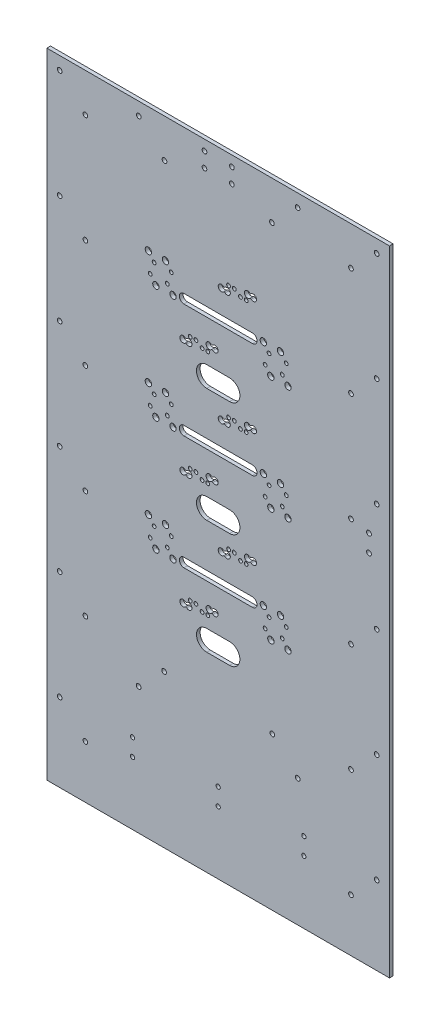
SolidWorks part; units mm, degrees
ref_plane "Front Plane" through (0, 0, 0) normal (0, 0, 1) x (1, 0, 0)
ref_plane "Top Plane" through (0, 0, 0) normal (0, 1, 0) x (1, 0, 0)
ref_plane "Right Plane" through (0, 0, 0) normal (1, 0, 0) x (0, 0, -1)
sketch "Sketch1" plane through (0, 0, 0) normal (0, 0, 1) x (1, 0, 0)
  line L0 (-165.9868, 389.7156) -> (134.0132, 389.7156) construction
  line L1 (-165.9868, 389.7156) -> (134.0132, 389.7156)
  line L2 (-165.9868, 389.7156) -> (-165.9868, -165.2844)
  line L3 (-165.9868, -165.2844) -> (134.0132, -165.2844)
  line L4 (134.0132, 389.7156) -> (134.0132, -165.2844)
  line L5 (89.0132, -165.2844) -> (134.0132, -165.2844) construction
  line L6 (134.0132, 389.7156) -> (134.0132, -165.2844) construction
  dimension "D2" = 300
extrude "Boss-Extrude1" add sketch "Sketch1" along normal blind 3.175
sketch "Sketch2" plane through (0, 0, 0) normal (0, 0, -1) x (-1, 0, 0)
  line L0 (15.9868, -165.2844) -> (15.9868, 389.7156) construction
  line L1 (165.9868, -165.2844) -> (-134.0132, -165.2844) construction
  line L2 (-134.0132, 389.7156) -> (165.9868, 389.7156) construction
  line L3 (0.9868, 59.7156) -> (30.9868, 59.7156) construction
  line L4 (0.9868, 159.7156) -> (30.9868, 159.7156) construction
  line L5 (0.9868, 259.7156) -> (30.9868, 259.7156) construction
  point P8 (15.9868, 59.7156)
  point P11 (15.9868, 159.7156)
  dimension "D1" = 30
  dimension "D2" = 30
  dimension "D3" = 100
  dimension "D4" = 100
  dimension "D5" = 130
sketch "Sketch4" plane through (0, 0, 3.175) normal (0, 0, 1) x (1, 0, 0)
  line L0 (-45.9868, 259.7156) -> (14.0132, 259.7156) construction
  line L1 (-45.9868, 263.7156) -> (14.0132, 263.7156)
  line L2 (-45.9868, 255.7156) -> (14.0132, 255.7156)
  line L3 (-15.9868, -165.2844) -> (-15.9868, 389.7156) construction
  line L4 (-0.9868, 259.7156) -> (-30.9868, 259.7156) construction
  line L5 (-45.9868, 159.7156) -> (14.0132, 159.7156) construction
  line L6 (-45.9868, 163.7156) -> (14.0132, 163.7156)
  line L7 (-45.9868, 155.7156) -> (14.0132, 155.7156)
  line L8 (-45.9868, 59.7156) -> (14.0132, 59.7156) construction
  line L9 (-45.9868, 63.7156) -> (14.0132, 63.7156)
  line L10 (-45.9868, 55.7156) -> (14.0132, 55.7156)
  line L11 (-0.9868, 59.7156) -> (-30.9868, 59.7156) construction
  line L12 (-0.9868, 159.7156) -> (-30.9868, 159.7156) construction
  arc A0 (-45.9868, 263.7156) -> (-45.9868, 255.7156) centre (-45.9868, 259.7156) ccw
  arc A1 (14.0132, 255.7156) -> (14.0132, 263.7156) centre (14.0132, 259.7156) ccw
  arc A2 (-45.9868, 163.7156) -> (-45.9868, 155.7156) centre (-45.9868, 159.7156) ccw
  arc A3 (14.0132, 155.7156) -> (14.0132, 163.7156) centre (14.0132, 159.7156) ccw
  arc A4 (-45.9868, 63.7156) -> (-45.9868, 55.7156) centre (-45.9868, 59.7156) ccw
  arc A5 (14.0132, 55.7156) -> (14.0132, 63.7156) centre (14.0132, 59.7156) ccw
  point P2 (-15.9868, 259.7156)
  point P14 (-15.9868, 159.7156)
  point P21 (-15.9868, 59.7156)
  dimension "D1" = 15
  dimension "D2" = 8
  dimension "D3" = 15
  dimension "D4" = 8
  dimension "D5" = 15
  dimension "D6" = 8
extrude "Cut-Extrude1" cut sketch "Sketch4" against normal blind 10
sketch "Sketch5" plane through (0, 0, 0) normal (0, 0, -1) x (-1, 0, 0)
  line L0 (45.9868, 155.7156) -> (-14.0132, 155.7156) construction
sketch "Sketch6" plane through (0, 0, 0) normal (0, 0, -1) x (-1, 0, 0)
  line L0 (-134.0132, 389.7156) -> (165.9868, 389.7156) construction
  circle A0 centre (3.9868, 380.7156) radius 2.05
  circle A1 centre (27.9868, 380.7156) radius 2.05
  circle A2 centre (27.9868, 367.7156) radius 2.05
  circle A3 centre (3.9868, 367.7156) radius 2.05
  point P12 (42.9868, 389.7156)
  dimension "D1" = 15
  dimension "D2" = 4.1
  dimension "D3" = 39
  dimension "D4" = 9
  dimension "D5" = 22
extrude "Cut-Extrude5" cut sketch "Sketch6" against normal blind 51
sketch "Sketch8" plane through (0, 0, 0) normal (0, 0, -1) x (-1, 0, 0)
  circle A0 centre (-116.0132, 162.9803) radius 2.1
  circle A1 centre (-116.0132, 147.9803) radius 2.1
  point P6 (0, 0)
  point P7 (0, 0)
  dimension "D1" = 4.2
extrude "Cut-Extrude7" cut sketch "Sketch8" against normal blind 67
sketch "Sketch9" plane through (0, 0, 0) normal (0, 0, -1) x (-1, 0, 0)
  line L0 (15.9868, 389.7156) -> (15.9868, 432.1874) construction
  line L1 (-134.0132, 389.7156) -> (165.9868, 389.7156) construction
  circle A0 centre (-122.7632, 378.4656) radius 2.05
  circle A1 centre (-100.2632, 355.9656) radius 2.05
  circle A2 centre (-53.5368, 378.4656) radius 2.05
  circle A3 centre (-31.0368, 355.9656) radius 2.05
  circle A4 centre (-122.7632, 283.4656) radius 2.05
  circle A5 centre (-100.2632, 260.9656) radius 2.05
  circle A6 centre (-122.7632, 188.4656) radius 2.05
  circle A7 centre (-100.2632, 165.9656) radius 2.05
  circle A8 centre (-122.7632, 93.4656) radius 2.05
  circle A9 centre (-100.2632, 70.9656) radius 2.05
  circle A10 centre (-122.7632, -1.5344) radius 2.05
  circle A11 centre (-100.2632, -24.0344) radius 2.05
  circle A12 centre (-122.7632, -96.5344) radius 2.05
  circle A13 centre (-100.2632, -119.0344) radius 2.05
  circle A14 centre (-122.7632, -191.5344) radius 2.05
  circle A15 centre (-100.2632, -214.0344) radius 2.05
  circle A16 centre (-53.6482, -54.0344) radius 2.05
  circle A17 centre (-31.371, -31.5344) radius 2.05
  circle A18 centre (63.3447, -31.5344) radius 2.05
  circle A19 centre (85.6219, -54.0344) radius 2.05
  circle A20 centre (132.2368, -214.0344) radius 2.05
  circle A21 centre (154.7368, -191.5344) radius 2.05
  circle A22 centre (132.2368, -119.0344) radius 2.05
  circle A23 centre (154.7368, -96.5344) radius 2.05
  circle A24 centre (132.2368, -24.0344) radius 2.05
  circle A25 centre (154.7368, -1.5344) radius 2.05
  circle A26 centre (132.2368, 70.9656) radius 2.05
  circle A27 centre (154.7368, 93.4656) radius 2.05
  circle A28 centre (132.2368, 165.9656) radius 2.05
  circle A29 centre (154.7368, 188.4656) radius 2.05
  circle A30 centre (132.2368, 260.9656) radius 2.05
  circle A31 centre (154.7368, 283.4656) radius 2.05
  circle A32 centre (63.0104, 355.9656) radius 2.05
  circle A33 centre (85.5104, 378.4656) radius 2.05
  circle A34 centre (132.2368, 355.9656) radius 2.05
  circle A35 centre (154.7368, 378.4656) radius 2.05
  dimension "D1" = 7
extrude "Cut-Extrude8" cut sketch "Sketch9" against normal blind 10
sketch "Sketch10" plane through (0, 0, 0) normal (0, 0, -1) x (-1, 0, 0)
  circle A0 centre (35.464, 33.6216) radius 1.651
  circle A1 centre (25.1051, 30.1602) radius 1.651
  arc A2 (43.5999, 30.6974) -> (43.5999, 26.4941) centre (41.7588, 28.5958) ccw
  arc A3 (20.6514, 37.2877) -> (20.6514, 33.0844) centre (18.8103, 35.186) ccw
  circle A4 centre (-30.1263, 38.9336) radius 2.794
  circle A5 centre (-23.5434, 61.8842) radius 2.794
  circle A6 centre (-25.1024, 45.23) radius 1.651
  circle A7 centre (-28.5672, 55.5878) radius 1.651
  circle A8 centre (-45.1263, 38.9336) radius 2.794
  circle A9 centre (-38.5434, 61.8842) radius 2.794
  circle A10 centre (-40.1024, 45.23) radius 1.651
  circle A11 centre (-43.5672, 55.5878) radius 1.651
  circle A12 centre (40.464, 33.6216) radius 1.651
  circle A13 centre (30.1051, 30.1602) radius 1.651
  arc A14 (44.9177, 26.4941) -> (44.9177, 30.6974) centre (46.7588, 28.5958) ccw
  arc A15 (21.9693, 33.0844) -> (21.9693, 37.2877) centre (23.8103, 35.186) ccw
  arc A16 (21.9693, 33.0844) -> (20.6514, 33.0844) centre (21.3103, 32.3322) ccw
  arc A17 (21.9693, 37.2877) -> (20.6514, 37.2877) centre (21.3103, 38.0399) cw
  arc A18 (44.9177, 26.4941) -> (43.5999, 26.4941) centre (44.2588, 25.7419) ccw
  arc A19 (44.9177, 30.6974) -> (43.5999, 30.6974) centre (44.2588, 31.4496) cw
  circle A40 centre (55.5171, 57.5469) radius 2.794
  circle A41 centre (70.5171, 57.5469) radius 2.794
  circle A42 centre (75.5409, 63.8433) radius 1.651
  circle A43 centre (60.5409, 63.8433) radius 1.651
  circle A44 centre (-3.4904, 85.8095) radius 1.651
  circle A45 centre (6.8686, 89.271) radius 1.651
  arc A46 (-11.6262, 88.7337) -> (-11.6262, 92.937) centre (-9.7851, 90.8353) ccw
  arc A47 (11.3223, 82.1435) -> (11.3223, 86.3468) centre (13.1633, 84.2451) ccw
  circle A48 centre (62.0999, 80.4975) radius 2.794
  circle A49 centre (57.0761, 74.2011) radius 1.651
  circle A50 centre (77.0999, 80.4975) radius 2.794
  circle A51 centre (72.0761, 74.2011) radius 1.651
  circle A52 centre (-8.4904, 85.8095) radius 1.651
  circle A53 centre (1.8686, 89.271) radius 1.651
  arc A54 (-12.9441, 92.937) -> (-12.9441, 88.7337) centre (-14.7851, 90.8353) ccw
  arc A55 (10.0044, 86.3468) -> (10.0044, 82.1435) centre (8.1633, 84.2451) ccw
  arc A56 (10.0044, 86.3468) -> (11.3223, 86.3468) centre (10.6633, 87.099) ccw
  arc A57 (10.0044, 82.1435) -> (11.3223, 82.1435) centre (10.6633, 81.3913) cw
  arc A58 (-12.9441, 92.937) -> (-11.6262, 92.937) centre (-12.2851, 93.6892) ccw
  arc A59 (-12.9441, 88.7337) -> (-11.6262, 88.7337) centre (-12.2851, 87.9815) cw
  circle A60 centre (63.0104, 355.9656) radius 2.05 construction
  circle A62 centre (35.464, 133.6216) radius 1.651
  circle A63 centre (25.1051, 130.1602) radius 1.651
  arc A64 (43.5999, 130.6974) -> (43.5999, 126.4941) centre (41.7588, 128.5958) ccw
  arc A65 (20.6514, 137.2877) -> (20.6514, 133.0844) centre (18.8103, 135.186) ccw
  circle A66 centre (-30.1263, 138.9336) radius 2.794
  circle A67 centre (-23.5434, 161.8842) radius 2.794
  circle A68 centre (-25.1024, 145.23) radius 1.651
  circle A69 centre (-28.5672, 155.5878) radius 1.651
  circle A70 centre (-45.1263, 138.9336) radius 2.794
  circle A71 centre (-38.5434, 161.8842) radius 2.794
  circle A72 centre (-40.1024, 145.23) radius 1.651
  circle A73 centre (-43.5672, 155.5878) radius 1.651
  circle A74 centre (40.464, 133.6216) radius 1.651
  circle A75 centre (30.1051, 130.1602) radius 1.651
  arc A76 (44.9177, 126.4941) -> (44.9177, 130.6974) centre (46.7588, 128.5958) ccw
  arc A77 (21.9693, 133.0844) -> (21.9693, 137.2877) centre (23.8103, 135.186) ccw
  arc A78 (21.9693, 133.0844) -> (20.6514, 133.0844) centre (21.3103, 132.3322) ccw
  arc A79 (21.9693, 137.2877) -> (20.6514, 137.2877) centre (21.3103, 138.0399) cw
  arc A80 (44.9177, 126.4941) -> (43.5999, 126.4941) centre (44.2588, 125.7419) ccw
  arc A81 (44.9177, 130.6974) -> (43.5999, 130.6974) centre (44.2588, 131.4496) cw
  circle A82 centre (55.5171, 157.5469) radius 2.794
  circle A83 centre (70.5171, 157.5469) radius 2.794
  circle A84 centre (75.5409, 163.8433) radius 1.651
  circle A85 centre (60.5409, 163.8433) radius 1.651
  circle A86 centre (-3.4904, 185.8095) radius 1.651
  circle A87 centre (6.8686, 189.271) radius 1.651
  arc A88 (-11.6262, 188.7337) -> (-11.6262, 192.937) centre (-9.7851, 190.8353) ccw
  arc A89 (11.3223, 182.1435) -> (11.3223, 186.3468) centre (13.1633, 184.2451) ccw
  circle A90 centre (62.0999, 180.4975) radius 2.794
  circle A91 centre (57.0761, 174.2011) radius 1.651
  circle A92 centre (77.0999, 180.4975) radius 2.794
  circle A93 centre (72.0761, 174.2011) radius 1.651
  circle A94 centre (-8.4904, 185.8095) radius 1.651
  circle A95 centre (1.8686, 189.271) radius 1.651
  arc A96 (-12.9441, 192.937) -> (-12.9441, 188.7337) centre (-14.7851, 190.8353) ccw
  arc A97 (10.0044, 186.3468) -> (10.0044, 182.1435) centre (8.1633, 184.2451) ccw
  arc A98 (10.0044, 186.3468) -> (11.3223, 186.3468) centre (10.6633, 187.099) ccw
  arc A99 (10.0044, 182.1435) -> (11.3223, 182.1435) centre (10.6633, 181.3913) cw
  arc A100 (-12.9441, 192.937) -> (-11.6262, 192.937) centre (-12.2851, 193.6892) ccw
  arc A101 (-12.9441, 188.7337) -> (-11.6262, 188.7337) centre (-12.2851, 187.9815) cw
  circle A102 centre (35.464, 233.6216) radius 1.651
  circle A103 centre (25.1051, 230.1602) radius 1.651
  arc A104 (43.5999, 230.6974) -> (43.5999, 226.4941) centre (41.7588, 228.5958) ccw
  arc A105 (20.6514, 237.2877) -> (20.6514, 233.0844) centre (18.8103, 235.186) ccw
  circle A106 centre (-30.1263, 238.9336) radius 2.794
  circle A107 centre (-23.5434, 261.8842) radius 2.794
  circle A108 centre (-25.1024, 245.23) radius 1.651
  circle A109 centre (-28.5672, 255.5878) radius 1.651
  circle A110 centre (-45.1263, 238.9336) radius 2.794
  circle A111 centre (-38.5434, 261.8842) radius 2.794
  circle A112 centre (-40.1024, 245.23) radius 1.651
  circle A113 centre (-43.5672, 255.5878) radius 1.651
  circle A114 centre (40.464, 233.6216) radius 1.651
  circle A115 centre (30.1051, 230.1602) radius 1.651
  arc A116 (44.9177, 226.4941) -> (44.9177, 230.6974) centre (46.7588, 228.5958) ccw
  arc A117 (21.9693, 233.0844) -> (21.9693, 237.2877) centre (23.8103, 235.186) ccw
  arc A118 (21.9693, 233.0844) -> (20.6514, 233.0844) centre (21.3103, 232.3322) ccw
  arc A119 (21.9693, 237.2877) -> (20.6514, 237.2877) centre (21.3103, 238.0399) cw
  arc A120 (44.9177, 226.4941) -> (43.5999, 226.4941) centre (44.2588, 225.7419) ccw
  arc A121 (44.9177, 230.6974) -> (43.5999, 230.6974) centre (44.2588, 231.4496) cw
  circle A122 centre (55.5171, 257.5469) radius 2.794
  circle A123 centre (70.5171, 257.5469) radius 2.794
  circle A124 centre (75.5409, 263.8433) radius 1.651
  circle A125 centre (60.5409, 263.8433) radius 1.651
  circle A126 centre (-3.4904, 285.8095) radius 1.651
  circle A127 centre (6.8686, 289.271) radius 1.651
  arc A128 (-11.6262, 288.7337) -> (-11.6262, 292.937) centre (-9.7851, 290.8353) ccw
  arc A129 (11.3223, 282.1435) -> (11.3223, 286.3468) centre (13.1633, 284.2451) ccw
  circle A130 centre (62.0999, 280.4975) radius 2.794
  circle A131 centre (57.0761, 274.2011) radius 1.651
  circle A132 centre (77.0999, 280.4975) radius 2.794
  circle A133 centre (72.0761, 274.2011) radius 1.651
  circle A134 centre (-8.4904, 285.8095) radius 1.651
  circle A135 centre (1.8686, 289.271) radius 1.651
  arc A136 (-12.9441, 292.937) -> (-12.9441, 288.7337) centre (-14.7851, 290.8353) ccw
  arc A137 (10.0044, 286.3468) -> (10.0044, 282.1435) centre (8.1633, 284.2451) ccw
  arc A138 (10.0044, 286.3468) -> (11.3223, 286.3468) centre (10.6633, 287.099) ccw
  arc A139 (10.0044, 282.1435) -> (11.3223, 282.1435) centre (10.6633, 281.3913) cw
  arc A140 (-12.9441, 292.937) -> (-11.6262, 292.937) centre (-12.2851, 293.6892) ccw
  arc A141 (-12.9441, 288.7337) -> (-11.6262, 288.7337) centre (-12.2851, 287.9815) cw
  dimension "D3" = 1
  dimension "D4" = 1
  dimension "D5" = 3
  dimension "D1" = 2
  dimension "D2" = 2
extrude "Cut-Extrude9" cut sketch "Sketch10" against normal blind 10
sketch "Sketch12" plane through (0, 0, 0) normal (0, 0, -1) x (-1, 0, 0)
  circle A0 centre (90.9868, -95.2078) radius 1.85
  circle A1 centre (90.9868, -110.2078) radius 1.85
  circle A2 centre (15.9868, -95.2078) radius 1.85
  circle A3 centre (15.9868, -110.2078) radius 1.85
  circle A4 centre (-59.0132, -95.2078) radius 1.85
  circle A5 centre (-59.0132, -110.2078) radius 1.85
  dimension "D1" = 3
extrude "Cut-Extrude10" cut sketch "Sketch12" against normal blind 10
sketch "Sketch13" plane through (0, 0, 3.175) normal (0, 0, 1) x (1, 0, 0)
  line L0 (-15.9868, 55.7156) -> (-15.9868, 10.7156) construction
  line L1 (-45.9868, 55.7156) -> (14.0132, 55.7156) construction
  line L2 (-25.9868, 10.7156) -> (-5.9868, 10.7156) construction
  line L3 (-25.9868, 19.7156) -> (-5.9868, 19.7156)
  line L4 (-25.9868, 1.7156) -> (-5.9868, 1.7156)
  line L5 (14.0132, 63.7156) -> (-45.9868, 63.7156) construction
  line L6 (14.0132, 163.7156) -> (-45.9868, 163.7156) construction
  line L7 (-25.9868, 110.7156) -> (-5.9868, 110.7156) construction
  line L8 (-25.9868, 119.7156) -> (-5.9868, 119.7156)
  line L9 (-25.9868, 101.7156) -> (-5.9868, 101.7156)
  line L10 (-25.9868, 210.7156) -> (-5.9868, 210.7156) construction
  line L11 (-25.9868, 219.7156) -> (-5.9868, 219.7156)
  line L12 (-25.9868, 201.7156) -> (-5.9868, 201.7156)
  arc A0 (-25.9868, 19.7156) -> (-25.9868, 1.7156) centre (-25.9868, 10.7156) ccw
  arc A1 (-5.9868, 1.7156) -> (-5.9868, 19.7156) centre (-5.9868, 10.7156) ccw
  arc A2 (-25.9868, 119.7156) -> (-25.9868, 101.7156) centre (-25.9868, 110.7156) ccw
  arc A3 (-5.9868, 101.7156) -> (-5.9868, 119.7156) centre (-5.9868, 110.7156) ccw
  arc A4 (-25.9868, 219.7156) -> (-25.9868, 201.7156) centre (-25.9868, 210.7156) ccw
  arc A5 (-5.9868, 201.7156) -> (-5.9868, 219.7156) centre (-5.9868, 210.7156) ccw
  point P6 (-15.9868, 10.7156)
  point P19 (-15.9868, 110.7156)
  point P26 (-15.9868, 210.7156)
  dimension "D1" = 18
  dimension "D2" = 45
  dimension "D3" = 20
  dimension "D4" = 100
  dimension "D6" = 100
  dimension "D5" = 3
extrude "Cut-Extrude11" cut sketch "Sketch13" against normal blind 29.1
